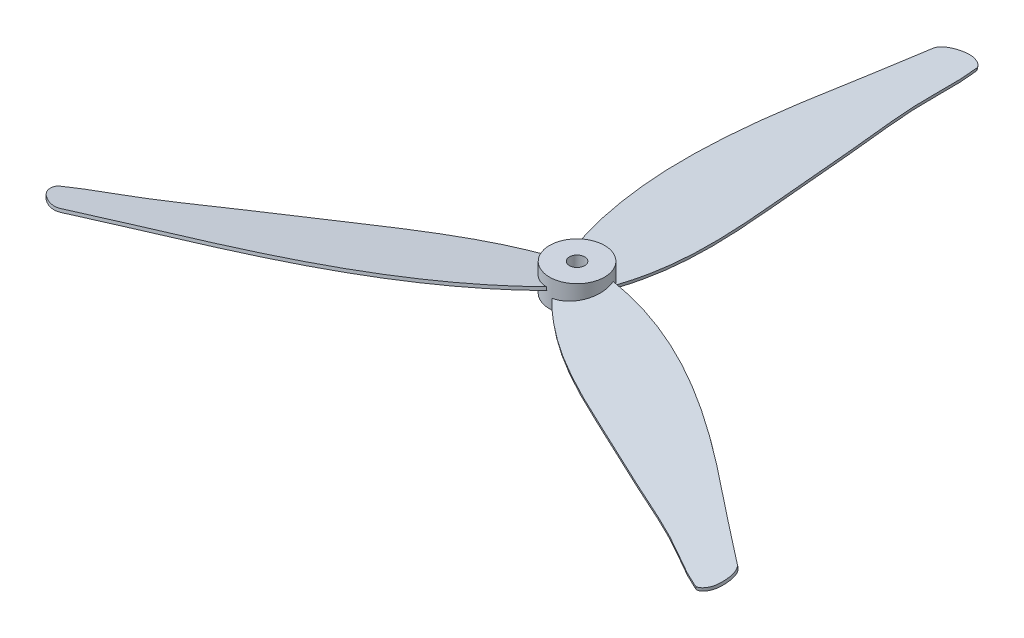
SolidWorks part; units mm, degrees
material "A-Glass Fiber"
ref_plane "Front Plane" through (0, 0, 0) normal (0, 0, 1) x (1, 0, 0)
ref_plane "Top Plane" through (0, 0, 0) normal (0, 1, 0) x (1, 0, 0)
ref_plane "Right Plane" through (0, 0, 0) normal (1, 0, 0) x (0, 0, -1)
sketch "Sketch1" plane through (0, 0, 0) normal (0, 1, 0) x (1, 0, 0)
  circle A0 centre (0, 0) radius 9
  circle A1 centre (0, 0) radius 2.5
  dimension "D1" = 18
  dimension "D2" = 5
extrude "Boss-Extrude1" add sketch "Sketch1" along normal blind 9
sketch "Sketch3" plane through (0, 0, 0) normal (0, 1, 0) x (1, 0, 0)
  line L0 (0, 0) -> (0, 32.3409) construction
  line L1 (0, 0) -> (86.3188, -49.8362) construction
  dimension "D1" = 120
ref_plane "Plane1" through (0, 0, 0) normal (-0.0782, 0.9877, 0.1355) x (0.866, 0, 0.5)
sketch "Sketch2" plane through (0, 0, 0) normal (0.0782, -0.9877, -0.1355) x (0.5031, -0.0782, 0.8607)
  line L0 (-0.0729, 0) -> (109.2834, -64.577) construction
  arc A3 (7.0572, 3.5223) -> (-0.8103, -7.8456) centre (0, 0) cw
  spline S0 degree 3 poles (-0.8103, -7.8456) (14.8456, -26.5282) (50.11, -46.9687) (87.5823, -60.2779) (104.3944, -67.4966) (108.6947, -65.6224) (111.8395, -62.2937) (111.6744, -59.1449) (110.3348, -58.1895) (105.388, -54.6473) (93.4703, -48.5314) (77.381, -36.6533) (48.7521, -17.4899) (26.9641, -1.2792) (7.0572, 3.5223) knots 0 0 0 0 0.282933 0.466483 0.471857 0.495006 0.514383 0.523355 0.526651 0.533187 0.595375 0.682473 0.767936 1 1 1 1
  dimension "D1" = 127
extrude "Boss-Extrude2" add sketch "Sketch2" along normal blind 1 from offset 4.5 offset against normal yes
pattern_circular "CirPattern1" count 3 over 360 about axis through (0, 9, 0) along (0, 1, 0) of "Boss-Extrude2"
move or copy body "Body-Move/Copy1" [suppressed] bodies to move or copy 103 parameters "D1"=0, "D2"=0, "D3"=0
